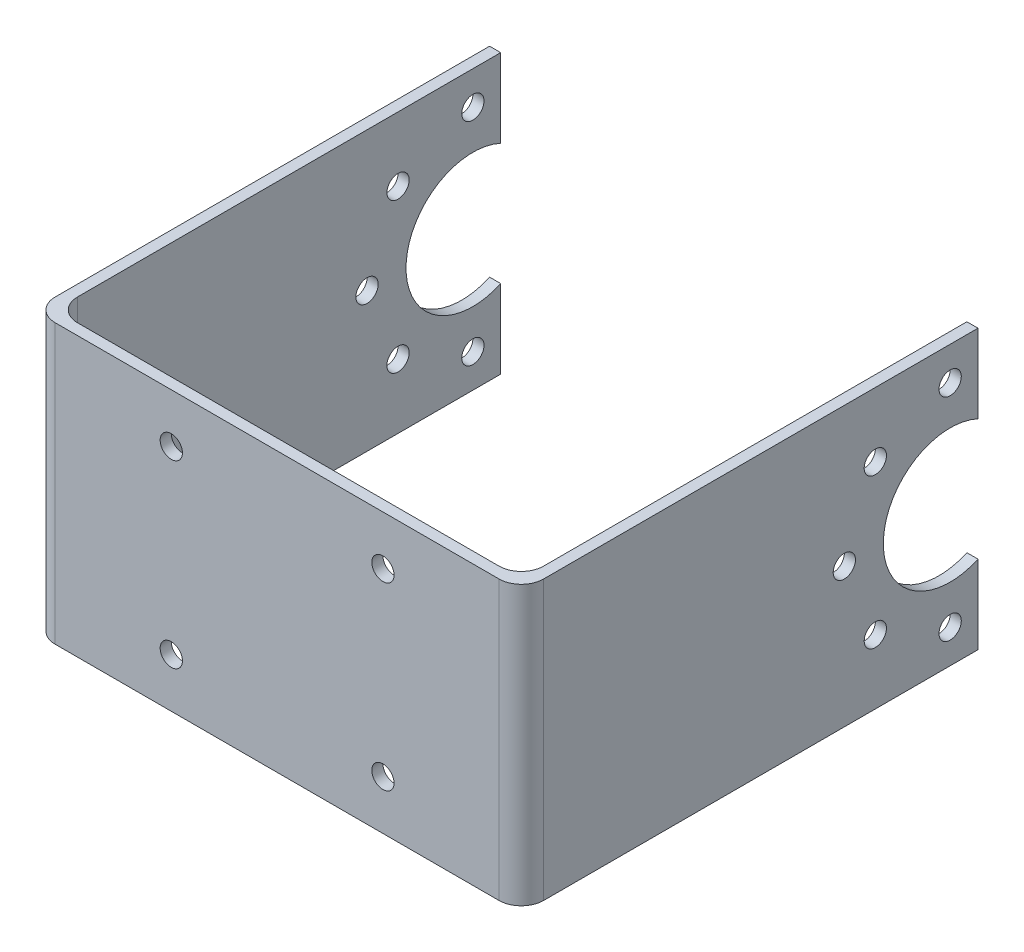
SolidWorks part; units mm, degrees
material "1060 Alloy"
ref_plane "Front Plane" through (0, 0, 0) normal (0, 0, 1) x (1, 0, 0)
ref_plane "Top Plane" through (0, 0, 0) normal (0, 1, 0) x (1, 0, 0)
ref_plane "Right Plane" through (0, 0, 0) normal (1, 0, 0) x (0, 0, -1)
sketch "Sketch1" plane through (0, 0, 0) normal (0, 1, 0) x (1, 0, 0)
  line L1 (-21.5, 0.5) -> (20.35, 0.5)
  line L2 (-22.5, 0.5) -> (-22.5, -0.5)
  line L3 (-22.5, -0.5) -> (21.35, -0.5)
  line L4 (21.35, 0.5) -> (21.35, -0.5)
  line L8 (21.35, 0.5) -> (21.35, 40.5)
  line L9 (21.35, 40.5) -> (20.35, 40.5)
  line L10 (20.35, 0.5) -> (20.35, 40.5)
  line L12 (-22.5, 0.5) -> (-22.5, 40.5)
  line L13 (-22.5, 40.5) -> (-21.5, 40.5)
  line L14 (-21.5, 0.5) -> (-21.5, 40.5)
  point P0 (0, 0)
  dimension "D1" = 43.85
  dimension "D2" = 1
  dimension "D3" = 1
  dimension "D4" = 1
  dimension "D5" = 40
  dimension "D6" = 40
extrude "Boss-Extrude1" add sketch "Sketch1" along normal blind 25
sketch "Sketch2" plane through (21.35, 0, 0) normal (1, 0, 0) x (0, 0, -1)
  line L1 (40.5, 12.5) -> (38, 12.5)
  line L2 (40.5, 25) -> (40.5, 0) construction
  line L3 (32, 12.5) -> (28.5, 12.5)
  circle A0 centre (38, 12.5) radius 6
  circle A1 centre (28.5, 12.5) radius 1
  circle A2 centre (31.2825, 19.2175) radius 1
  circle A3 centre (38, 22) radius 1
  circle A4 centre (44.7175, 19.2175) radius 1
  circle A5 centre (47.5, 12.5) radius 1
  circle A6 centre (44.7175, 5.7825) radius 1
  circle A7 centre (38, 3) radius 1
  circle A8 centre (31.2825, 5.7825) radius 1
  point P25 (38, 12.5)
  dimension "D1" = 2.5
  dimension "D3" = 3.5
  dimension "D2" = 12
  dimension "D4" = 2
  dimension "D5" = 8
extrude "Cut-Extrude1" cut sketch "Sketch2" against normal through all
fillet "Fillet2" radius 2 4 edges at (-22.5, 12.5, 0.5) (-21.5, 12.5, -0.5) (21.35, 12.5, 0.5) (20.35, 12.5, -0.5)
sketch "Sketch3" plane through (0, 0, 0.5) normal (0, 0, 1) x (1, 0, 0)
  line L0 (-0.575, 25) -> (-0.575, 20.585)
  line L1 (-0.575, 4.415) -> (-0.575, 0)
  line L2 (-0.575, 20.585) -> (-10.075, 20.585)
  line L3 (-0.575, 20.585) -> (8.925, 20.585)
  line L4 (-20.5, 25) -> (19.35, 25) construction
  line L5 (-20.5, 0) -> (19.35, 0) construction
  line L8 (-0.575, 4.415) -> (-10.075, 4.415)
  line L9 (-0.575, 4.415) -> (8.925, 4.415)
  circle A0 centre (-10.075, 20.585) radius 1
  circle A1 centre (8.925, 20.585) radius 1
  circle A2 centre (-10.075, 4.415) radius 1
  circle A3 centre (8.925, 4.415) radius 1
  dimension "D3" = 2
  dimension "D4" = 2
  dimension "D9" = 2
  dimension "D10" = 2
  dimension "D1" = 9.5
  dimension "D2" = 9.5
  dimension "D5" = 4.415
  dimension "D6" = 4.415
  dimension "D7" = 9.5
  dimension "D8" = 9.5
extrude "Cut-Extrude2" cut sketch "Sketch3" against normal through all
